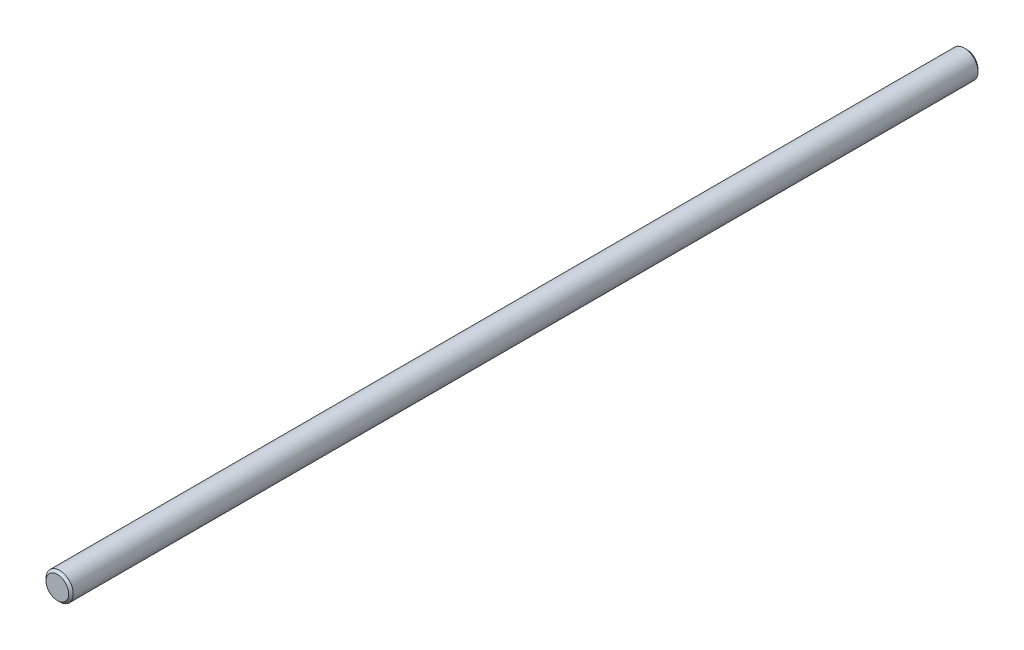
SolidWorks part; units mm, degrees
material "AISI 304"
ref_plane "Спереди" through (0, 0, 0) normal (0, 0, 1) x (1, 0, 0)
ref_plane "Сверху" through (0, 0, 0) normal (0, 1, 0) x (1, 0, 0)
ref_plane "Справа" through (0, 0, 0) normal (1, 0, 0) x (0, 0, -1)
sketch "Эскиз1" plane through (0, 0, 0) normal (0, 0, 1) x (1, 0, 0)
  circle A0 centre (0, 0) radius 6
  dimension "D1" = 12
extrude "Бобышка-Вытянуть1" add sketch "Эскиз1" along normal blind 400
chamfer "Фаска1" distance 1 angle 45 2 edges at (6, 0, 0) (6, 0, 400)
